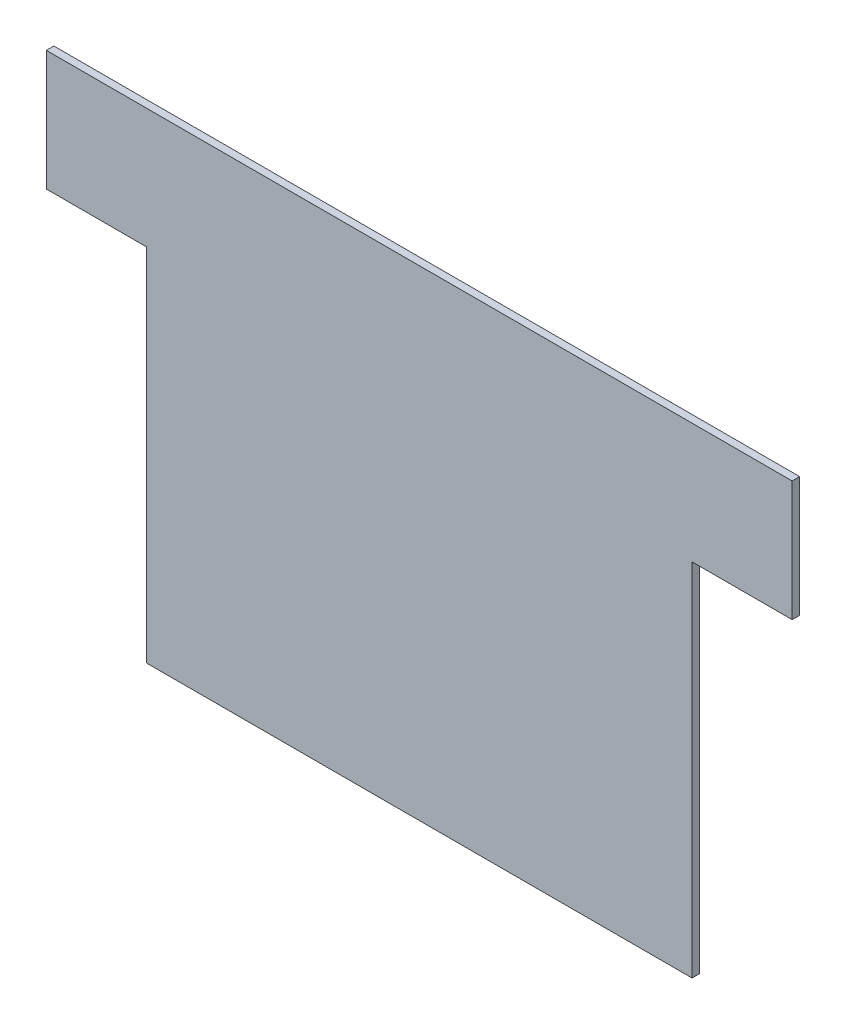
SolidWorks part; units mm, degrees
ref_plane "Front Plane" through (0, 0, 0) normal (0, 0, 1) x (1, 0, 0)
ref_plane "Top Plane" through (0, 0, 0) normal (0, 1, 0) x (1, 0, 0)
ref_plane "Right Plane" through (0, 0, 0) normal (1, 0, 0) x (0, 0, -1)
sketch "Sketch3" plane through (0, 0, 0) normal (0, 0, 1) x (1, 0, 0)
  line L0 (346.075, 228.6) -> (409.575, 228.6)
  line L1 (0, 0) -> (346.075, 0)
  line L2 (0, 0) -> (0, 228.6)
  line L4 (346.075, 0) -> (346.075, 228.6)
  line L5 (-63.5, 304.8) -> (409.575, 304.8)
  line L6 (-63.5, 304.8) -> (-63.5, 228.6)
  line L7 (-63.5, 228.6) -> (0, 228.6)
  line L8 (409.575, 304.8) -> (409.575, 228.6)
  dimension "D1" = 346.075
  dimension "D2" = 473.075
  dimension "D3" = 63.5
  dimension "D4" = 228.6
  dimension "D5" = 76.2
extrude "Boss-Extrude1" add sketch "Sketch3" along normal blind 4.7625
